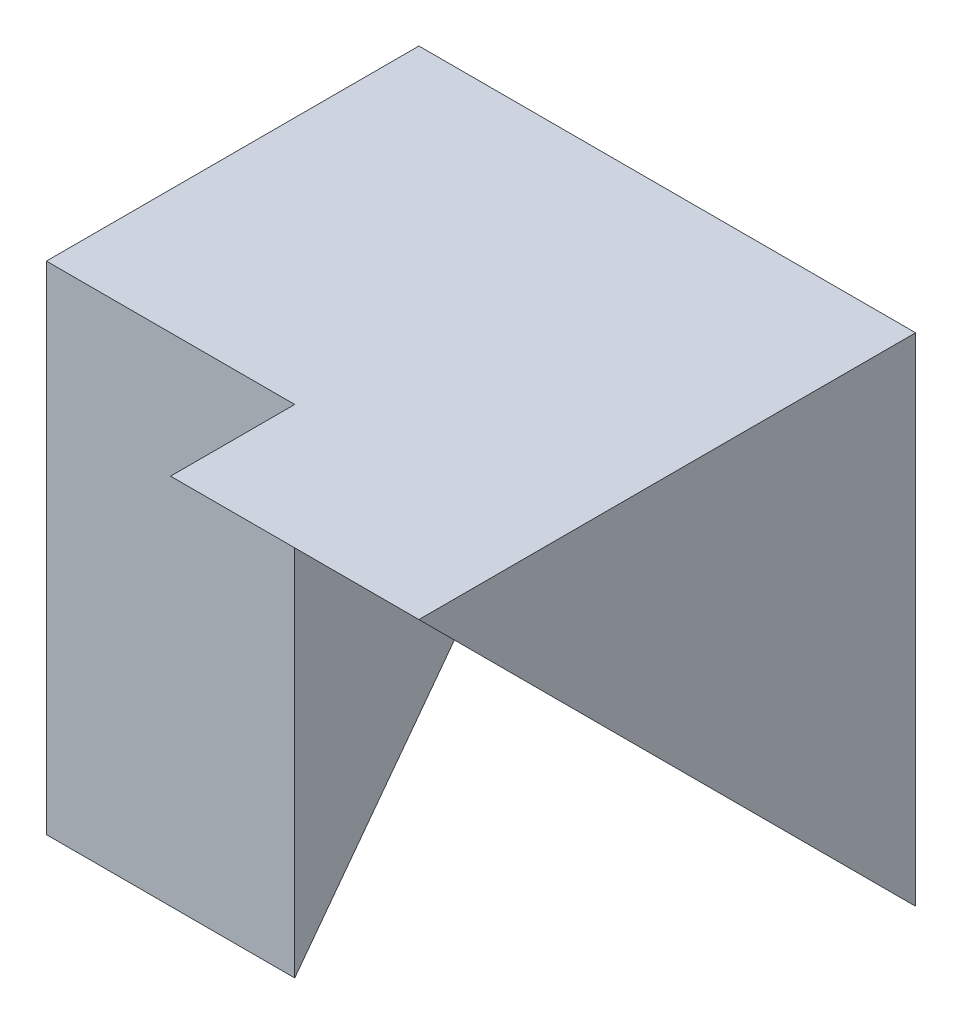
SolidWorks part; units mm, degrees
ref_plane "Front Plane" through (0, 0, 0) normal (0, 0, 1) x (1, 0, 0)
ref_plane "Top Plane" through (0, 0, 0) normal (0, 1, 0) x (1, 0, 0)
ref_plane "Right Plane" through (0, 0, 0) normal (1, 0, 0) x (0, 0, -1)
sketch "Sketch1" plane through (0, 0, 0) normal (1, 0, 0) x (0, 0, -1)
  line L1 (0, 0) -> (4, 0)
  line L2 (0, 0) -> (0, 4)
  line L3 (0, 4) -> (4, 4)
  line L4 (4, 0) -> (4, 4)
  dimension "D1" = 4
  dimension "D2" = 4
extrude "Boss-Extrude1" add sketch "Sketch1" along normal blind 2
sketch "Sketch2" plane through (0, 0, 0) normal (-1, 0, 0) x (0, 0, 1)
  line L0 (-1, 0) -> (-1, 4)
  line L1 (0, 0) -> (-4, 0) construction
  line L2 (-4, 0) -> (-4, 4) construction
  line L3 (-4, 4) -> (-4, 0)
  line L4 (-4, 0) -> (-1, 0)
  line L5 (-4, 4) -> (0, 4) construction
  line L6 (-1, 4) -> (-4, 4)
  dimension "D1" = 3
  dimension "D2" = 4
extrude "Boss-Extrude2" add sketch "Sketch2" along normal blind 2
sketch "Sketch3" plane through (2, 0, 0) normal (1, 0, 0) x (0, 0, -1)
  line L0 (4, 0) -> (0, 4)
  line L1 (0, 4) -> (0, 0) construction
  line L2 (0, 4) -> (4, 4)
  line L3 (4, 4) -> (4, 0)
  line M4 (0, 4) -> (0, 0)
  line M5 (0, 0) -> (4, 0)
extrude "Cut-Extrude1" cut sketch "Sketch3" against normal blind 2 contours L0 M5 M4
sketch "Sketch4" plane through (-2, 0, 0) normal (-1, 0, 0) x (0, 0, 1)
  line L0 (-1, 0) -> (-4, 4)
  line L1 (-4, 4) -> (-1, 4)
  line L2 (-1, 4) -> (-1, 0)
  line M4 (-4, 0) -> (-1, 0)
  line M7 (-4, 4) -> (-4, 0)
extrude "Cut-Extrude2" cut sketch "Sketch4" against normal blind 2 contours L0 M4 M7
